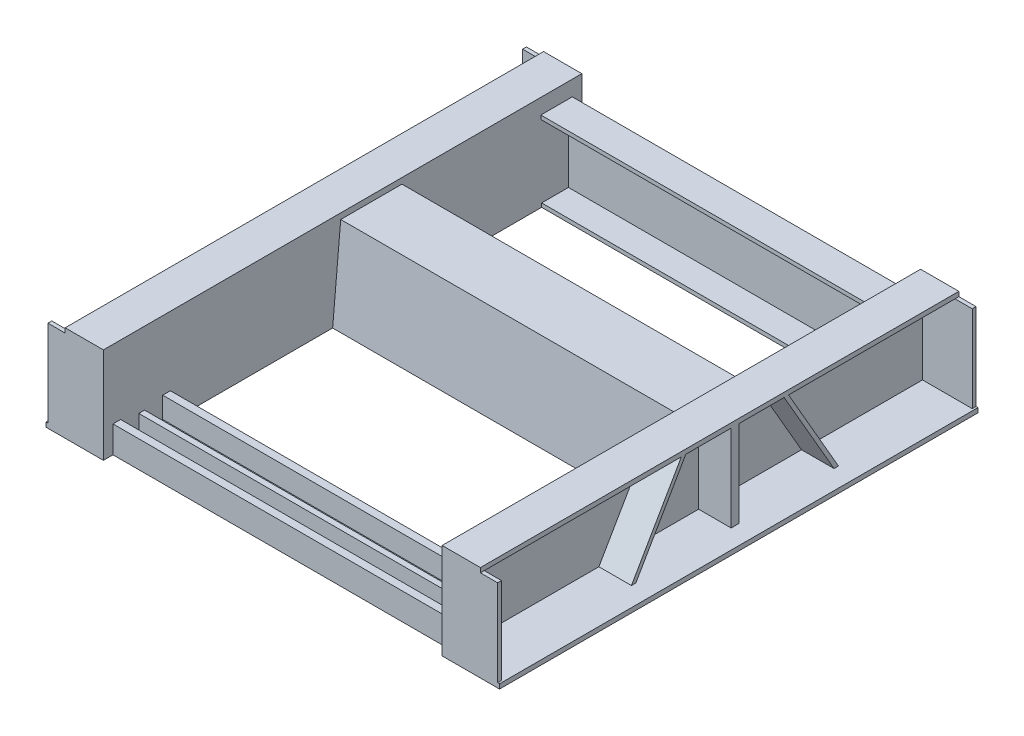
SolidWorks part; units mm, degrees
ref_plane "Front Plane" through (0, 0, 0) normal (0, 0, 1) x (1, 0, 0)
ref_plane "Top Plane" through (0, 0, 0) normal (0, 1, 0) x (1, 0, 0)
ref_plane "Right Plane" through (0, 0, 0) normal (1, 0, 0) x (0, 0, -1)
sketch "Sketch1" plane through (0, 0, 0) normal (0, 0, 1) x (1, 0, 0)
  line L0 (-74.2424, 0) -> (98.1818, 0) construction
  line L1 (0, 74.0909) -> (0, -102.8788) construction
  line L2 (72.7273, 62.0909) -> (72.7273, 74.0909)
  line L3 (72.7273, 74.0909) -> (-27.2727, 74.0909)
  line L4 (-27.2727, 74.0909) -> (-27.2727, -175.9091)
  line L8 (-12.2727, -163.9091) -> (-12.2727, 62.0909)
  line L9 (-12.2727, 62.0909) -> (72.7273, 62.0909)
  line L11 (122.7273, -175.9091) -> (122.7273, -163.9091)
  line L12 (122.7273, -163.9091) -> (-12.2727, -163.9091)
  line L13 (122.7273, -175.9091) -> (-27.2727, -175.9091)
  dimension "D1" = 12
  dimension "D2" = 250
  dimension "D3" = 15
  dimension "D4" = 12
  dimension "D5" = 150
  dimension "D6" = 100
extrude "Boss-Extrude1" add sketch "Sketch1" along normal blind 1250
sketch "Sketch2" plane through (-12.2727, 0, 0) normal (1, 0, 0) x (0, 0, -1)
  line L0 (-1250, -163.9091) -> (0, -163.9091) construction
  line L1 (-1240, -163.9091) -> (-1250, -163.9091)
  line L2 (-1240, -163.9091) -> (-1240, 62.0909)
  line L3 (-1240, 62.0909) -> (-1250, 62.0909)
  line L4 (-1250, -163.9091) -> (-1250, 62.0909)
  dimension "D1" = 10
extrude "Boss-Extrude2" add sketch "Sketch2" along normal blind 130
sketch "Sketch3" plane through (-12.2727, 0, 0) normal (1, 0, 0) x (0, 0, -1)
  line L0 (-1250, -163.9091) -> (0, -163.9091) construction
  line L1 (0, 62.0909) -> (-10, 62.0909)
  line L2 (0, 62.0909) -> (0, -163.9091)
  line L3 (0, -163.9091) -> (-10, -163.9091)
  line L4 (-10, 62.0909) -> (-10, -163.9091)
  dimension "D1" = 10
extrude "Boss-Extrude3" add sketch "Sketch3" along normal blind 130
sketch "Sketch5" plane through (0, 0, 1250) normal (0, 0, 1) x (1, 0, 0)
  line L0 (-27.2727, -175.9091) -> (122.7273, -175.9091) construction
  line L1 (-2.2727, -25.9091) -> (77.7273, -25.9091)
  line L2 (-2.2727, -25.9091) -> (-2.2727, -155.9091)
  line L3 (-2.2727, -155.9091) -> (77.7273, -155.9091)
  line L4 (77.7273, -25.9091) -> (77.7273, -155.9091)
  line L5 (117.7273, 62.0909) -> (117.7273, -163.9091) construction
  line L6 (-27.2727, 74.0909) -> (-27.2727, -175.9091) construction
  line L7 (72.7273, 74.0909) -> (-27.2727, 74.0909) construction
  point P10 (-2.2727, -90.9091)
  dimension "D1" = 20
  dimension "D2" = 40
  dimension "D3" = 25
  dimension "D4" = 100
extrude "Cut-Extrude1" cut sketch "Sketch5" against normal blind 130
sketch "Sketch8" plane through (-27.2727, 0, 0) normal (-1, 0, 0) x (0, 0, 1)
  line L0 (1095, -105.9091) -> (1095, -160.9091)
  line L1 (1095, -160.9091) -> (1142.5, -160.9091)
  line L2 (1142.5, -160.9091) -> (1142.5, -115.9091)
  line L3 (1142.5, -115.9091) -> (1157.5, -115.9091)
  line L4 (1157.5, -115.9091) -> (1157.5, -160.9091)
  line L5 (1157.5, -160.9091) -> (1205, -160.9091)
  line L6 (1205, -160.9091) -> (1205, -105.9091)
  line L7 (1205, -105.9091) -> (1225, -105.9091)
  line L8 (1225, -105.9091) -> (1225, -175.9091)
  line L9 (1250, -175.9091) -> (0, -175.9091) construction
  line L10 (1225, -175.9091) -> (1075, -175.9091)
  line L11 (1075, -175.9091) -> (1075, -105.9091)
  line L12 (1075, -105.9091) -> (1095, -105.9091)
  line L16 (480, 49.0909) -> (620, 49.0909)
  line L17 (480, 49.0909) -> (460, -175.9091)
  line L20 (470, 59.0909) -> (450, -175.9091)
  line L21 (630, 59.0909) -> (651.1215, -175.9091)
  line L22 (620, 49.0909) -> (641.1215, -175.9091)
  line L23 (450, -175.9091) -> (460, -175.9091)
  line L24 (641.1215, -175.9091) -> (651.1215, -175.9091)
  line L25 (470, 59.0909) -> (630, 59.0909)
  line L26 (0, -175.9091) -> (25, -175.9091)
  line L27 (25, -175.9091) -> (25, 34.0909)
  line L28 (25, 34.0909) -> (107.2058, 34.0909)
  line L29 (107.2058, 34.0909) -> (107.2058, 24.0909)
  line L30 (107.2058, 24.0909) -> (35, 24.0909)
  line L31 (35, 24.0909) -> (35, -165.9091)
  line L32 (35, -165.9091) -> (105, -165.9091)
  line L33 (105, -165.9091) -> (105, -175.9091)
  line L34 (105, -175.9091) -> (25, -175.9091)
  line M10 (0, -175.9091) -> (1250, -175.9091)
sketch "Sketch9" plane through (-27.2727, 0, 0) normal (-1, 0, 0) x (0, 0, 1)
  line L0 (0, -175.9091) -> (25, -175.9091)
  line L1 (1250, -175.9091) -> (0, -175.9091) construction
extrude "Boss-Extrude4" add sketch "Sketch8" along normal blind 442.5 contours L33 L32 L31 L30 L29 L28 L27 M10 | L25 L20 L17 L16 L22 L21 M10 | L12 L11 L8 L7 L6 L5 L4 L3 L2 L1 L0 M10
ref_plane "Plane3" through (-469.7727, 0, 0) normal (-1, 0, 0) x (0, 0, 1)
mirror "Mirror5" about plane through (-469.7727, 0, 0) normal (-1, 0, 0) of "Boss-Extrude4", "Cut-Extrude1", "Boss-Extrude3", "Boss-Extrude2", "Boss-Extrude1"
mirror "Mirror6" about plane through (-469.7727, 0, 0) normal (-1, 0, 0) of "Boss-Extrude3", "Boss-Extrude2", "Boss-Extrude1"
mirror "Mirror8" about plane through (-469.7727, 0, 0) normal (-1, 0, 0) of "Cut-Extrude1"
sketch "Sketch12" plane through (-927.2727, 0, 0) normal (-1, 0, 0) x (0, 0, 1)
  line L0 (10, -50.9091) -> (1240, -50.9091) construction
  line L1 (10, 62.0909) -> (10, -163.9091) construction
  line L2 (1240, -163.9091) -> (1240, 62.0909) construction
  line L3 (625, 62.0909) -> (625, -175.9091) construction
  line L4 (1240, 62.0909) -> (10, 62.0909) construction
  line L5 (1250, -175.9091) -> (0, -175.9091) construction
  line L9 (575, 62.0909) -> (575, -163.9091)
  line L10 (595, 62.0909) -> (595, -163.9091)
  line L11 (575, 62.0909) -> (595, 62.0909)
  line L12 (575, -163.9091) -> (595, -163.9091)
sketch "Sketch13" plane through (-927.2727, 0, 0) normal (-1, 0, 0) x (0, 0, 1)
  line L0 (445, 62.0909) -> (725, 62.0909)
  line L1 (1240, 62.0909) -> (10, 62.0909) construction
  line L2 (445, 62.0909) -> (314.5188, -163.9091)
  line L3 (1250, -163.9091) -> (0, -163.9091) construction
  line L4 (1240, 62.0909) -> (10, 62.0909) construction
  line L5 (716.3397, 57.0909) -> (843.9342, -163.9091)
  line L6 (725, 62.0909) -> (855.4812, -163.9091)
  line L7 (1240, -163.9091) -> (10, -163.9091) construction
  line L11 (716.3397, 57.0909) -> (713.453, 62.0909)
  line L12 (314.5188, -163.9091) -> (855.4812, -163.9091)
  line L13 (716.3397, 57.0909) -> (846.8209, -168.9091) construction
  line L14 (453.6603, 57.0909) -> (326.0658, -163.9091)
  line L15 (453.6603, 57.0909) -> (456.547, 62.0909)
  line L16 (453.6603, 57.0909) -> (323.1791, -168.9091) construction
  line M12 (10, -163.9091) -> (1240, -163.9091)
  line M14 (1240, 62.0909) -> (10, 62.0909)
  dimension "D1" = 60
  dimension "D2" = 60
  dimension "D3" = 10
  dimension "D4" = 10
extrude "Boss-Extrude5" add sketch "Sketch13" along normal blind 85 contours L14 L15 L2 M14 M12 | L11 L5 L6 M12 M14
extrude "Boss-Extrude6" add sketch "Sketch12" along normal blind 85
mirror "Mirror9" about plane through (-469.7727, 0, 0) normal (-1, 0, 0) of "Mirror6", "Boss-Extrude5", "Boss-Extrude6"
